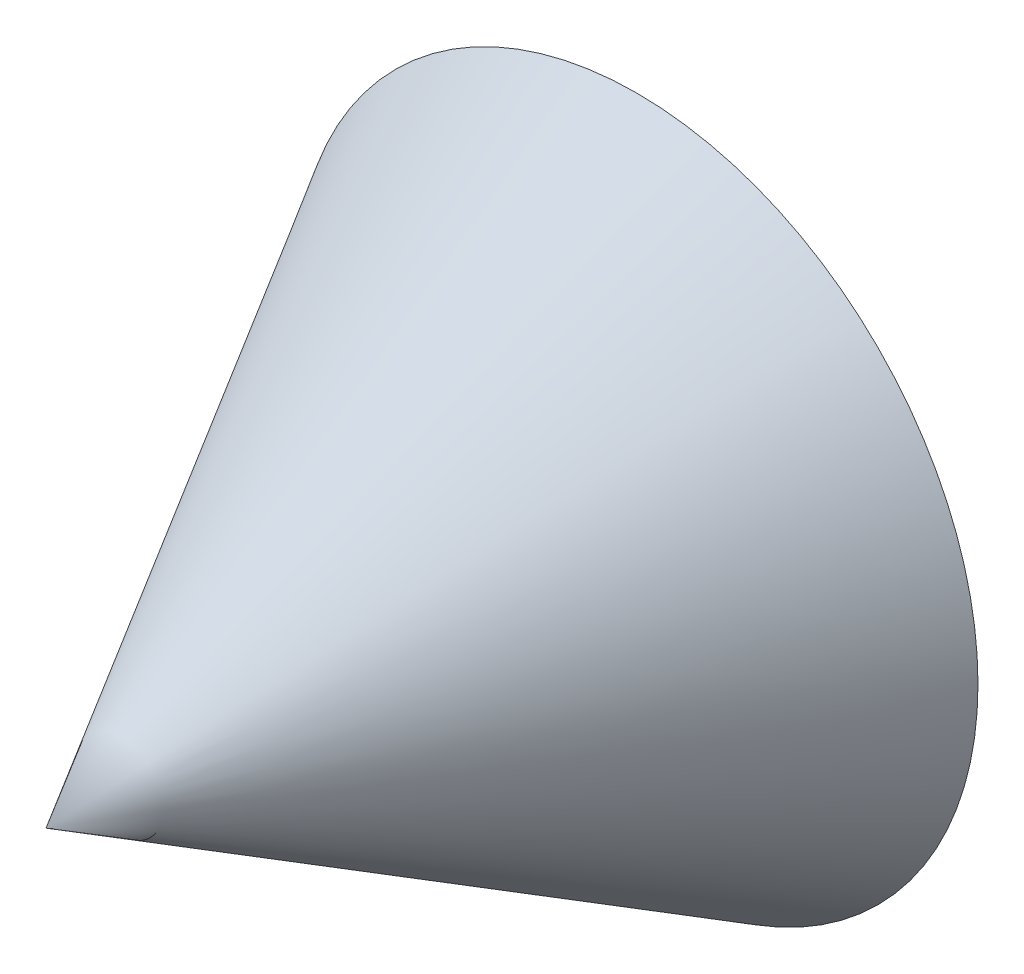
SolidWorks part; units mm, degrees
ref_plane "Front Plane" through (0, 0, 0) normal (0, 0, 1) x (1, 0, 0)
ref_plane "Top Plane" through (0, 0, 0) normal (0, 1, 0) x (1, 0, 0)
ref_plane "Right Plane" through (0, 0, 0) normal (1, 0, 0) x (0, 0, -1)
sketch "Sketch1" plane through (0, 0, 0) normal (0, 1, 0) x (1, 0, 0)
  line L0 (0, 0) -> (0, 200)
  line L1 (0, 200) -> (115.4701, 200)
  line L2 (115.4701, 200) -> (0, 0)
  dimension "D1" = 30
  dimension "D2" = 200
revolve "Revolve1" add sketch "Sketch1" angle 360 about L0
